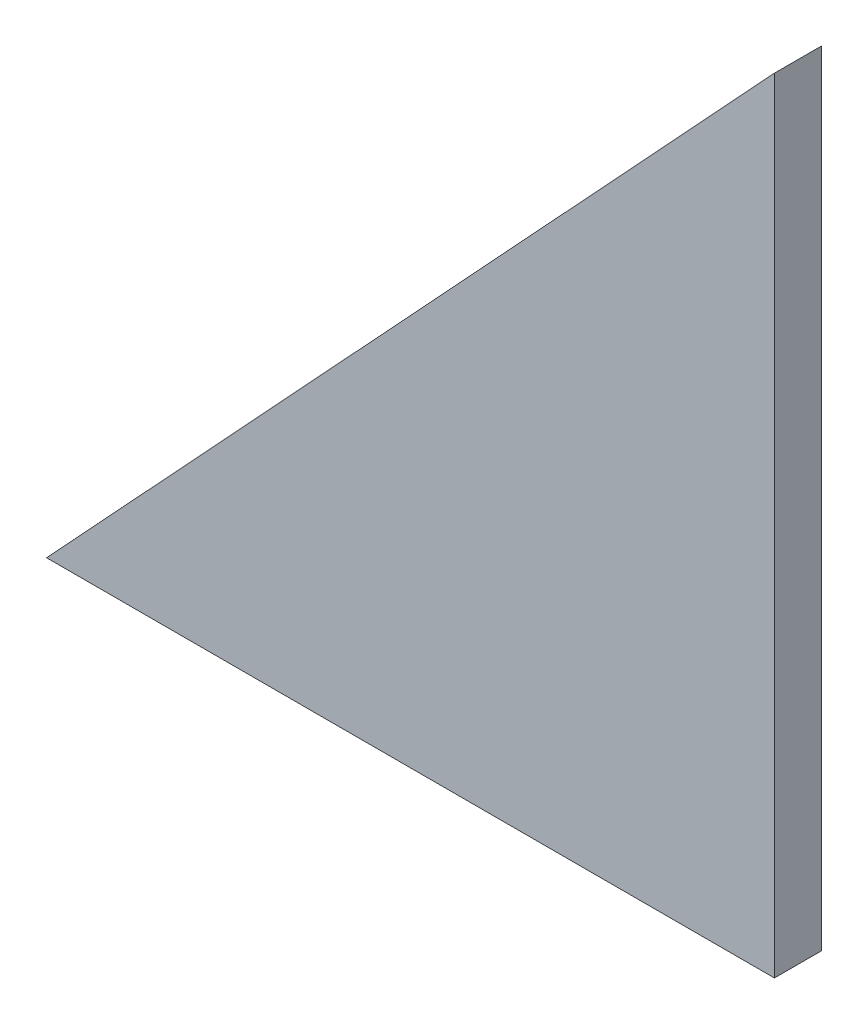
SolidWorks part; units mm, degrees
ref_plane "Płaszczyzna przednia" through (0, 0, 0) normal (0, 0, 1) x (1, 0, 0)
ref_plane "Płaszczyzna górna" through (0, 0, 0) normal (0, 1, 0) x (1, 0, 0)
ref_plane "Płaszczyzna prawa" through (0, 0, 0) normal (1, 0, 0) x (0, 0, -1)
ref_plane "Płaszczyzna1" through (0, 0, -1.5) normal (0, 0, -1) x (-1, 0, 0)
sketch "Szkic1" plane through (0, 0, -1.5) normal (0, 0, -1) x (-1, 0, 0)
  line L1 (23.22, 0) -> (0, 25)
  line L2 (0, 25) -> (0, 0)
  line L3 (0, 0) -> (23.22, 0)
  dimension "D1" = 23.22
  dimension "D2" = 25
extrude "Dodanie-wyciągnięcie1" add sketch "Szkic1" against normal blind 2
sketch "Szkic2" plane through (0, 0, 0) normal (0, -1, 0) x (-1, 0, 0)
  circle A0 centre (-6.78, 11.5015) radius 12.5
  dimension "D1" = 25
  dimension "D2" = 30
  dimension "D3" = 12.0015
extrude "Wytnij-wyciągnięcie1" cut sketch "Szkic2" against normal blind 25
